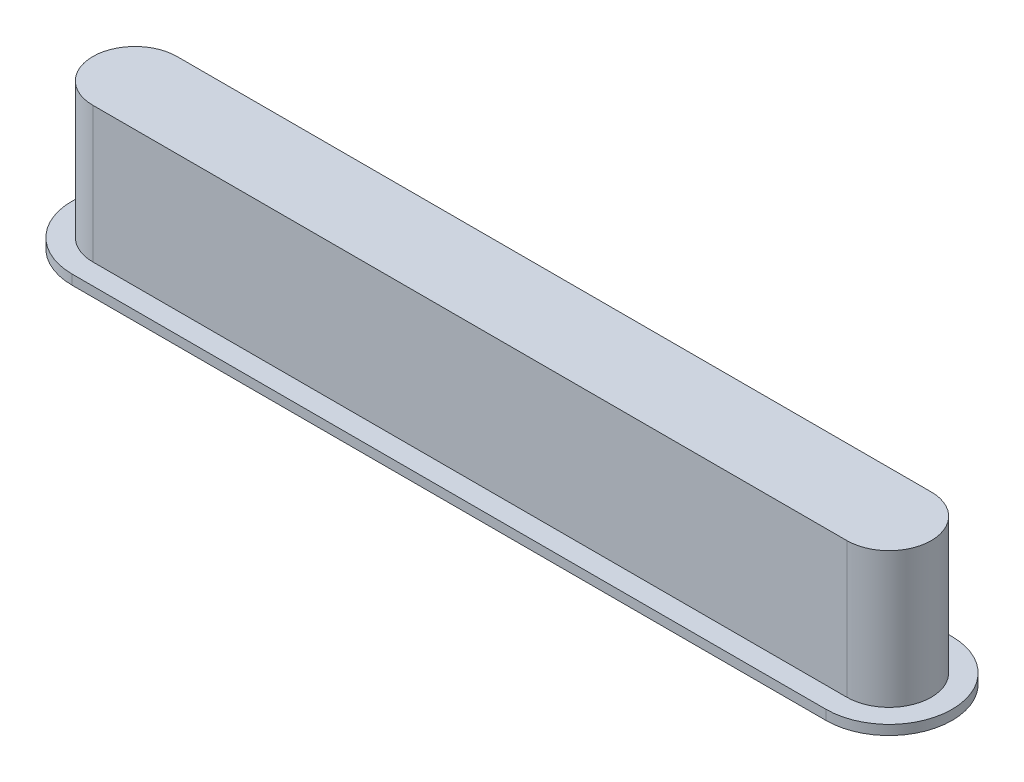
SolidWorks part; units mm, degrees
ref_plane "Front Plane" through (0, 0, 0) normal (0, 0, 1) x (1, 0, 0)
ref_plane "Top Plane" through (0, 0, 0) normal (0, 1, 0) x (1, 0, 0)
ref_plane "Right Plane" through (0, 0, 0) normal (1, 0, 0) x (0, 0, -1)
sketch "Sketch1" plane through (0, 0, 0) normal (0, 1, 0) x (1, 0, 0)
  line L0 (-9.8806, 0) -> (9.8806, 0) construction
  line L1 (-9.8806, 1.1049) -> (9.8806, 1.1049)
  line L2 (-9.8806, -1.1049) -> (9.8806, -1.1049)
  arc A0 (-9.8806, 1.1049) -> (-9.8806, -1.1049) centre (-9.8806, 0) ccw
  arc A1 (9.8806, -1.1049) -> (9.8806, 1.1049) centre (9.8806, 0) ccw
  point P2 (0, 0)
  dimension "D1" = 21.971
  dimension "D2" = 2.2098
  dimension "D3" = 19.7612
extrude "Boss-Extrude1" add sketch "Sketch1" along normal blind 3.556
sketch "Sketch3" plane through (0, 0, 0) normal (0, 1, 0) x (1, 0, 0)
  line L0 (-9.8806, 0) -> (9.8806, 0) construction
  line L1 (-9.8806, 1.651) -> (9.8806, 1.651)
  line L2 (-9.8806, -1.651) -> (9.8806, -1.651)
  arc A0 (-9.8806, 1.651) -> (-9.8806, -1.651) centre (-9.8806, 0) ccw
  arc A1 (9.8806, -1.651) -> (9.8806, 1.651) centre (9.8806, 0) ccw
  point P2 (0, 0)
  dimension "D1" = 3.302
extrude "Boss-Extrude2" add sketch "Sketch3" against normal blind 0.254
